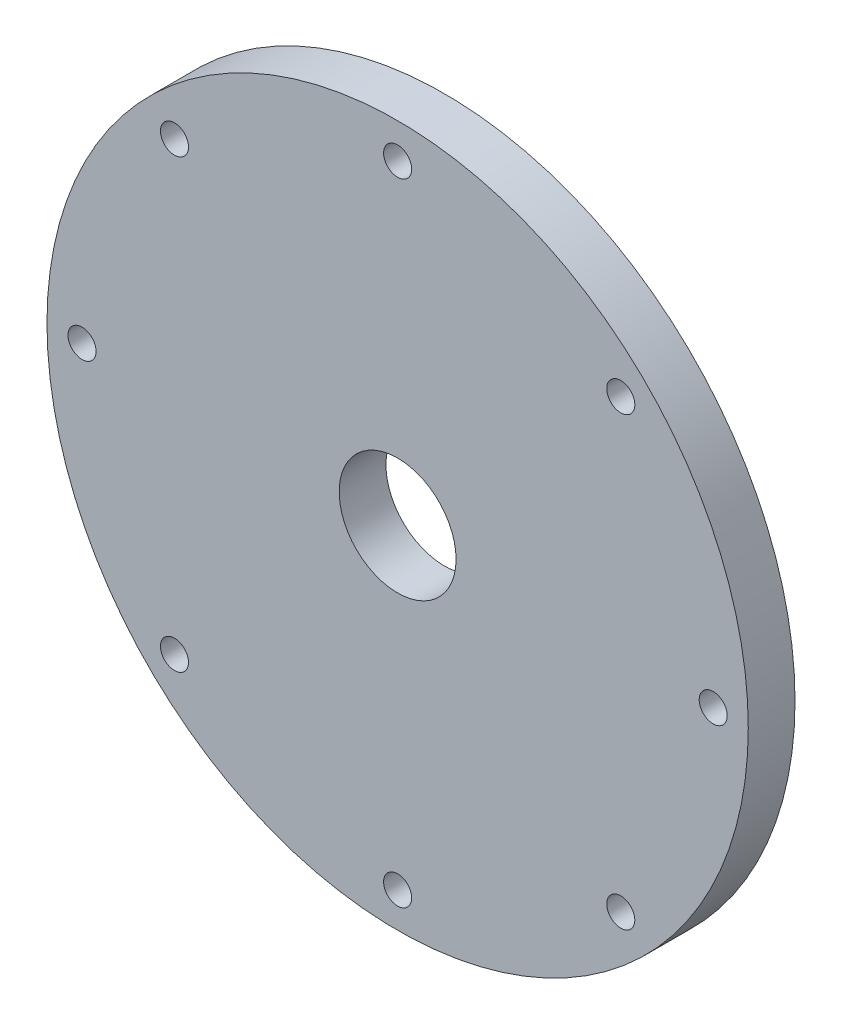
SolidWorks part; units mm, degrees
ref_plane "Alzado" through (0, 0, 0) normal (0, 0, 1) x (1, 0, 0)
ref_plane "Planta" through (0, 0, 0) normal (0, 1, 0) x (1, 0, 0)
ref_plane "Vista lateral" through (0, 0, 0) normal (1, 0, 0) x (0, 0, -1)
sketch "Croquis1" plane through (0, 0, 0) normal (0, 0, 1) x (1, 0, 0)
  circle A0 centre (0, 0) radius 75
  circle A1 centre (0, 0) radius 67.5 construction
  circle A2 centre (0, 67.5) radius 3
  circle A3 centre (47.7297, 47.7297) radius 3
  circle A4 centre (67.5, 0) radius 3
  circle A5 centre (47.7297, -47.7297) radius 3
  circle A6 centre (0, -67.5) radius 3
  circle A7 centre (-47.7297, -47.7297) radius 3
  circle A8 centre (-67.5, 0) radius 3
  circle A9 centre (-47.7297, 47.7297) radius 3
  circle A10 centre (0, 0) radius 12.5
  point P22 (0, 0)
  dimension "D1" = 135
  dimension "D2" = 150
  dimension "D3" = 6
  dimension "D5" = 25
  dimension "D4" = 8
extrude "Saliente-Extruir1" add sketch "Croquis1" along normal blind 10
